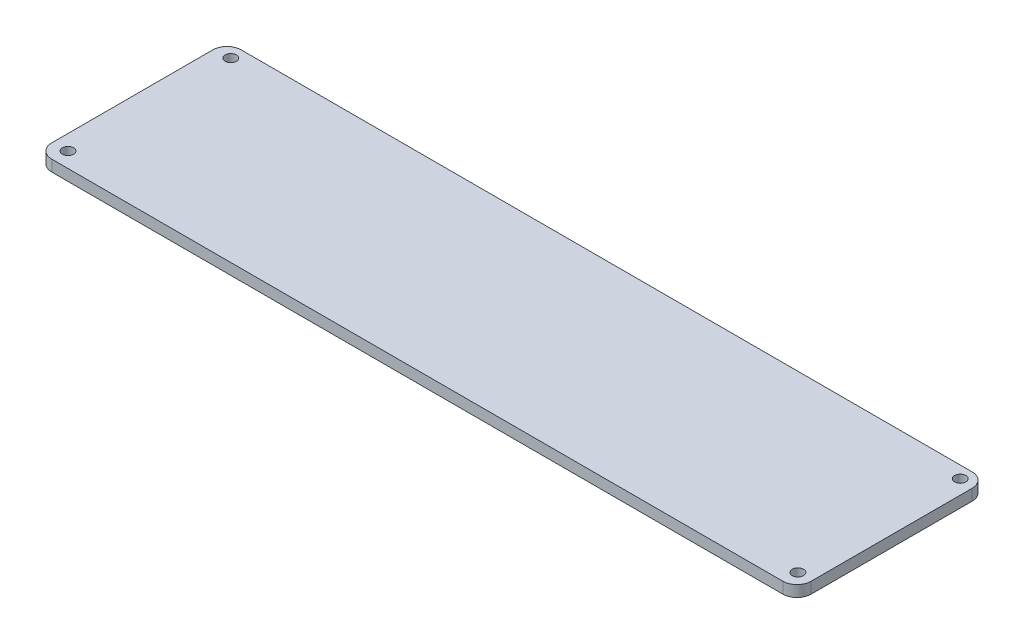
SolidWorks part; units mm, degrees
ref_plane "前视基准面" through (0, 0, 0) normal (0, 0, 1) x (1, 0, 0)
ref_plane "上视基准面" through (0, 0, 0) normal (0, 1, 0) x (1, 0, 0)
ref_plane "右视基准面" through (0, 0, 0) normal (1, 0, 0) x (0, 0, -1)
sketch "草图1" plane through (0, 0, 0) normal (0, 1, 0) x (1, 0, 0)
  line L1 (-102.3864, -24.3535) -> (100.8136, -24.3535)
  line L2 (-102.3864, -24.3535) -> (-102.3864, 26.3195)
  line L3 (-102.3864, 26.3195) -> (100.8136, 26.3195)
  line L4 (100.8136, -24.3535) -> (100.8136, 26.3195)
  line L29 (-91.2574, -24.3535) -> (-81.2574, -24.3535)
  circle A0 centre (-98.3224, -20.2895) radius 1.5
  circle A1 centre (-98.0684, 23.0175) radius 1.5
  circle A2 centre (97.0036, 23.1445) radius 1.5
  circle A3 centre (97.0036, -20.2895) radius 1.5
  point P41 (-71.1444, -5.3035)
  point P46 (-86.2574, -20.6705)
  point P61 (-10.3864, -24.3535)
  dimension "D5" = 3
  dimension "D8" = 3
  dimension "D11" = 3
  dimension "D14" = 3
  dimension "D1" = 203.2
  dimension "D2" = 50.673
  dimension "D3" = 4.064
  dimension "D4" = 4.064
  dimension "D6" = 4.318
  dimension "D7" = 3.302
  dimension "D9" = 3.81
  dimension "D10" = 3.175
  dimension "D12" = 3.81
  dimension "D13" = 4.064
  dimension "D38" = 31.242
  dimension "D39" = 19.05
  dimension "D42" = 3.683
  dimension "D43" = 16.129
  dimension "D53" = 92
extrude "凸台-拉伸1" add sketch "草图1" along normal blind 3 contours L1 L4 L3 L2 A3 A2 A1 A0
fillet "圆角1" radius 3.8 4 edges at (-102.3864, 1.5, -26.3195) (100.8136, 1.5, -26.3195) (100.8136, 1.5, 24.3535) (-102.3864, 1.5, 24.3535)
